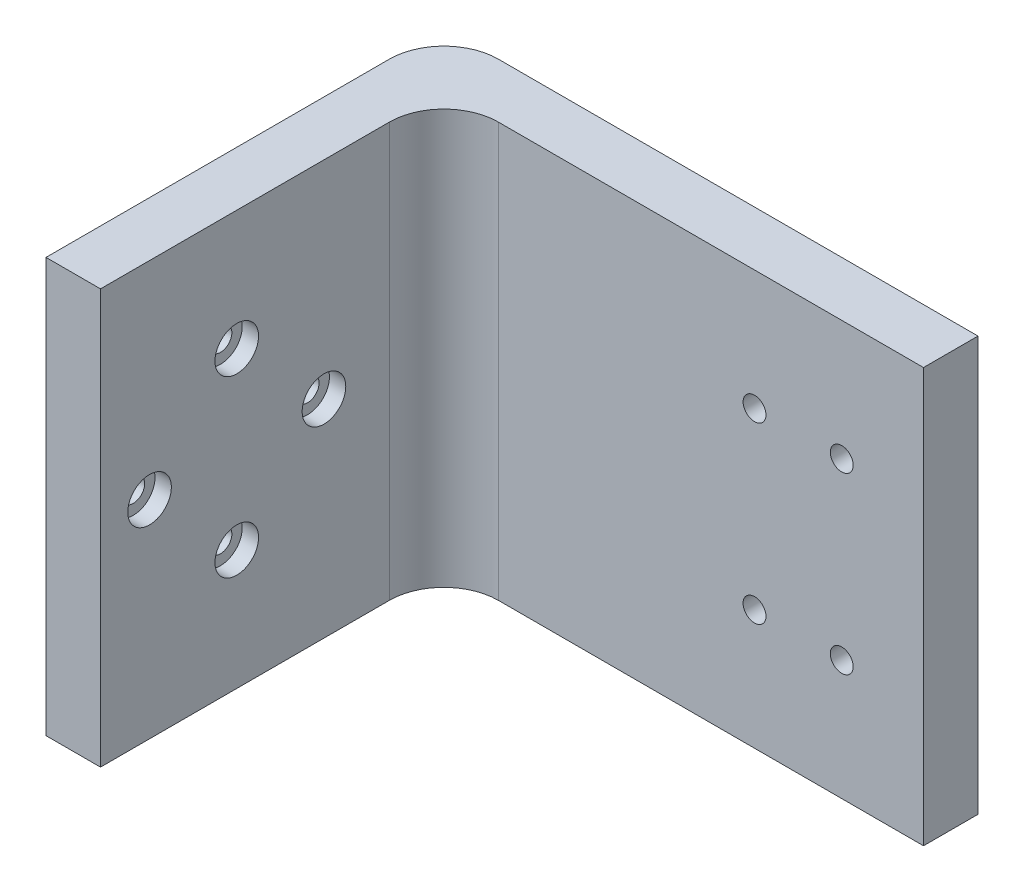
SolidWorks part; units mm, degrees
ref_plane "Front Plane" through (0, 0, 0) normal (0, 0, 1) x (1, 0, 0)
ref_plane "Top Plane" through (0, 0, 0) normal (0, 1, 0) x (1, 0, 0)
ref_plane "Right Plane" through (0, 0, 0) normal (1, 0, 0) x (0, 0, -1)
sketch "Sketch1" plane through (0, 0, 0) normal (1, 0, 0) x (0, 0, -1)
  line L6 (-12.5, 19) -> (-12.5, -19)
  line L16 (-12.5, -19) -> (19, -19)
  line L18 (19, 19) -> (-12.5, 19)
  line L20 (19, 19) -> (19, -19)
  arc A10 (1.05, 8) -> (-1.05, 8) centre (0, 8) ccw
  arc A11 (-1.05, 8) -> (1.05, 8) centre (0, 8) ccw
  arc A14 (6.95, 0) -> (9.05, 0) centre (8, 0) ccw
  arc A15 (9.05, 0) -> (6.95, 0) centre (8, 0) ccw
  arc A16 (-1.05, -8) -> (1.05, -8) centre (0, -8) ccw
  arc A17 (1.05, -8) -> (-1.05, -8) centre (0, -8) ccw
  arc A22 (-9.05, 0) -> (-6.95, 0) centre (-8, 0) ccw
  arc A23 (-6.95, 0) -> (-9.05, 0) centre (-8, 0) ccw
extrude "Boss-Extrude1" add sketch "Sketch1" along normal blind 5
sketch "Sketch3" plane through (0, 0, -19) normal (0, 0, -1) x (-1, 0, 0)
  line L0 (-5, -19) -> (0, -19) construction
  line L1 (0, 19) -> (-64, 19)
  line L2 (0, 19) -> (0, -19)
  line L3 (0, -19) -> (-64, -19)
  line L4 (-64, 19) -> (-64, -19)
  dimension "D1" = 64
  dimension "D2" = 0
extrude "Boss-Extrude3" add sketch "Sketch3" along normal blind 5 contours L1 L4 L3 L2
sketch "Sketch6" plane through (0, 0, -24) normal (0, 0, -1) x (-1, 0, 0)
  line L0 (-59, 17) -> (-34, 17)
  line L1 (-59, -17) -> (-34, -17)
  line L2 (-59, 17) -> (-68.1445, 17)
  line L3 (-59, -17) -> (-67.199, -17)
  line L7 (0, 26.0947) -> (-77.7041, 24.9392)
  line L8 (-77.7041, 24.9392) -> (-82.9567, -29.057)
  line L9 (-82.9567, -29.057) -> (-1.227, -34.0995)
  line L11 (-68.1445, 17) -> (-67.199, -17)
  line L12 (-34, 17) -> (-5, 19)
  line L13 (-34, -17) -> (-5, -19)
  line L14 (0, 26.0947) -> (-5, 19)
  line L15 (-5, -19) -> (-1.227, -34.0995)
extrude "Cut-Extrude2" [suppressed] cut sketch "Sketch6" against normal blind 5
sketch "Sketch7" plane through (0, 0, -19) normal (0, 0, 1) x (1, 0, 0)
  line L15 (33.5, 0) -> (42.4538, 0) construction
  arc A2 (41.5, -6.95) -> (41.5, -9.05) centre (41.5, -8) ccw
  arc A3 (41.5, -9.05) -> (41.5, -6.95) centre (41.5, -8) ccw
  arc A11 (41.5, 9.05) -> (41.5, 6.95) centre (41.5, 8) ccw
  arc A12 (41.5, 6.95) -> (41.5, 9.05) centre (41.5, 8) ccw
  circle A14 centre (33.5, 8) radius 1.05
  circle A15 centre (33.5, -8) radius 1.05
extrude "Cut-Extrude3" cut sketch "Sketch7" against normal blind 5
sketch "Sketch8" plane through (0, 0, -24) normal (0, 0, -1) x (-1, 0, 0)
  line L0 (0, 19) -> (-64, 19) construction
  line L1 (-64, -19) -> (-54, -19)
  line L2 (-64, -19) -> (-64, 19)
  line L3 (-64, 19) -> (-54, 19)
  line L4 (-54, -19) -> (-54, 19)
  dimension "D1" = 10
extrude "Cut-Extrude4" cut sketch "Sketch8" against normal blind 10
fillet "Fillet1" radius 5 2 edges at (0, 0, -24) (5, 0, -19)
sketch "Sketch9" plane through (0, 0, -24) normal (0, 0, -1) x (-1, 0, 0)
  circle A0 centre (-41.5, 8) radius 2
  circle A2 centre (-41.5, -8) radius 2
  circle A3 centre (-33.5, 8) radius 2
  circle A4 centre (-33.5, -8) radius 2
extrude "Cut-Extrude5" cut sketch "Sketch9" against normal blind 1.5
sketch "Sketch11" plane through (5, 0, 0) normal (1, 0, 0) x (0, 0, -1)
  circle A0 centre (0, 8) radius 2
  circle A1 centre (-8, 0) radius 2
  circle A2 centre (0, -8) radius 2
  circle A3 centre (8, 0) radius 2
extrude "Cut-Extrude7" cut sketch "Sketch11" against normal blind 1.5
sketch "Sketch12" plane through (0, 19, 0) normal (0, 1, 0) x (1, 0, 0)
  line L8 (54, 24) -> (49, 24)
  line L9 (5, 24) -> (54, 24) construction
  line L10 (49, 24) -> (49, 17.433)
  line L11 (49, 17.433) -> (56.6361, 15.9294)
  line L12 (56.6361, 15.9294) -> (56.3276, 23.5305)
  line L13 (56.3276, 23.5305) -> (54, 24)
extrude "Cut-Extrude8" cut sketch "Sketch12" against normal through all
